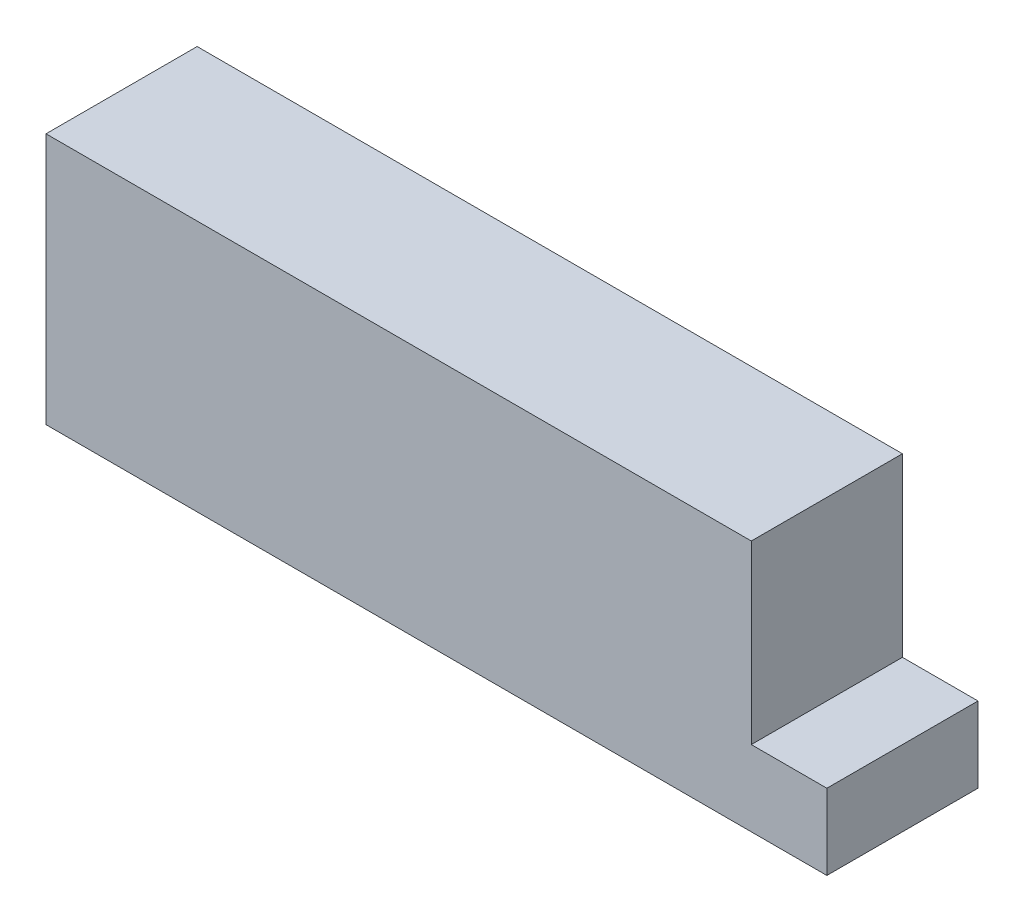
SolidWorks part; units mm, degrees
ref_plane "Plan de face" through (0, 0, 0) normal (0, 0, 1) x (1, 0, 0)
ref_plane "Plan de dessus" through (0, 0, 0) normal (0, 1, 0) x (1, 0, 0)
ref_plane "Plan de droite" through (0, 0, 0) normal (1, 0, 0) x (0, 0, -1)
sketch "Esquisse1" plane through (0, 0, 0) normal (0, 0, 1) x (1, 0, 0)
  line L1 (-63.4738, 34.5238) -> (76.5262, 34.5238)
  line L2 (-63.4738, 34.5238) -> (-63.4738, -15.4762)
  line L3 (-63.4738, -15.4762) -> (76.5262, -15.4762)
  line L4 (76.5262, 34.5238) -> (76.5262, -15.4762)
  dimension "D1" = 140
  dimension "D2" = 50
extrude "Boss.-Extru.1" add sketch "Esquisse1" along normal blind 30
sketch "Esquisse3" plane through (76.5262, 0, 0) normal (1, 0, 0) x (0, 0, -1)
  line L0 (-30, -15.4762) -> (0, -15.4762) construction
  line L1 (-30, -15.4762) -> (0, -15.4762)
  line L2 (-30, -15.4762) -> (-30, -0.4762)
  line L3 (-30, -0.4762) -> (0, -0.4762)
  line L4 (0, -15.4762) -> (0, -0.4762)
  dimension "D1" = 15
  dimension "D2" = 30
extrude "Boss.-Extru.2" add sketch "Esquisse3" along normal blind 15
